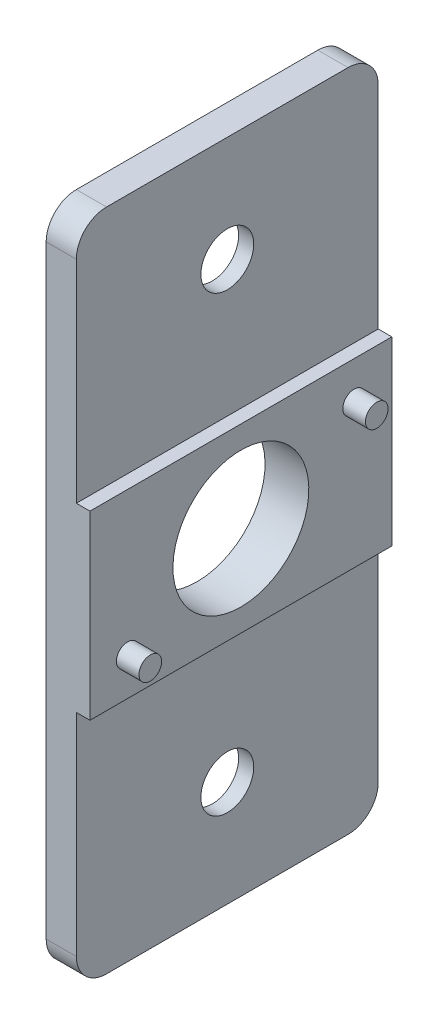
SolidWorks part; units mm, degrees
ref_plane "Front Plane" through (0, 0, 0) normal (0, 0, 1) x (1, 0, 0)
ref_plane "Top Plane" through (0, 0, 0) normal (0, 1, 0) x (1, 0, 0)
ref_plane "Right Plane" through (0, 0, 0) normal (1, 0, 0) x (0, 0, -1)
sketch "Sketch1" plane through (0, 0, 0) normal (0, 0, 1) x (1, 0, 0)
  line L0 (0, 0) -> (0, -44)
  line L1 (0, -44) -> (2, -44)
  line L2 (2, -44) -> (2, -28)
  line L3 (2, -28) -> (2.9, -28)
  line L4 (2.9, -28) -> (2.9, -16)
  line L5 (2.9, -16) -> (2, -16)
  line L6 (2, -16) -> (2, 0)
  line L7 (2, 0) -> (0, 0)
  line L8 (0, -22) -> (52.7304, -22) construction
  point P11 (2.9, -22)
  dimension "D1" = 2
  dimension "D2" = 44
  dimension "D3" = 12
  dimension "D4" = 0.9
extrude "Boss-Extrude1" add sketch "Sketch1" along normal blind 20
sketch "Sketch2" plane through (0, 0, 0) normal (-1, 0, 0) x (0, 0, 1)
  line L0 (10, 0) -> (10, -44) construction
  line L1 (20, 0) -> (0, 0) construction
  line L2 (20, -44) -> (0, -44) construction
  circle A0 centre (10, -7) radius 1.75
  circle A1 centre (10, -37) radius 1.75
  circle A2 centre (10, -22) radius 4.5
  dimension "D3" = 9
  dimension "D4" = 3.5
  dimension "D5" = 3.5
  dimension "D1" = 7
  dimension "D2" = 7
extrude "Cut-Extrude1" cut sketch "Sketch2" against normal through all
sketch "Sketch3" plane through (2.9, 0, 0) normal (1, 0, 0) x (0, 0, -1)
  line L1 (-20, -28) -> (-20, -16) construction
  line L2 (0, -28) -> (0, -16) construction
  line L4 (-20, -28) -> (0, -28) construction
  line L5 (-20, -16) -> (0, -16) construction
  circle A0 centre (-17.5, -25.5) radius 0.75
  circle A1 centre (-2.5, -18.5) radius 0.75
  dimension "D5" = 1.5
  dimension "D6" = 1.5
  dimension "D1" = 2.5
  dimension "D2" = 2.5
  dimension "D3" = 2.5
  dimension "D4" = 2.5
extrude "Boss-Extrude2" add sketch "Sketch3" along normal blind 1.5
fillet "Fillet1" radius 2 4 edges at (1, 0, 0) (1, 0, 20) (1, -44, 20) (1, -44, 0)
sketch "Sketch4" plane through (0, 0, 0) normal (-1, 0, 0) x (0, 0, 1)
  line L1 (11.8764, -10.25) -> (13.7528, -7)
  line L2 (13.7528, -7) -> (11.8764, -3.75)
  line L3 (11.8764, -3.75) -> (8.1236, -3.75)
  line L4 (8.1236, -3.75) -> (6.2472, -7)
  line L5 (6.2472, -7) -> (8.1236, -10.25)
  line L6 (8.1236, -10.25) -> (11.8764, -10.25)
  line L7 (11.8764, -40.25) -> (13.7528, -37)
  line L8 (13.7528, -37) -> (11.8764, -33.75)
  line L9 (11.8764, -33.75) -> (8.1236, -33.75)
  line L10 (8.1236, -33.75) -> (6.2472, -37)
  line L11 (6.2472, -37) -> (8.1236, -40.25)
  line L12 (8.1236, -40.25) -> (11.8764, -40.25)
  circle A0 centre (10, -7) radius 3.25 construction
  circle A1 centre (10, -37) radius 3.25 construction
  dimension "D1" = 6.5
  dimension "D2" = 6.5
extrude "Cut-Extrude2" cut sketch "Sketch4" against normal blind 1
